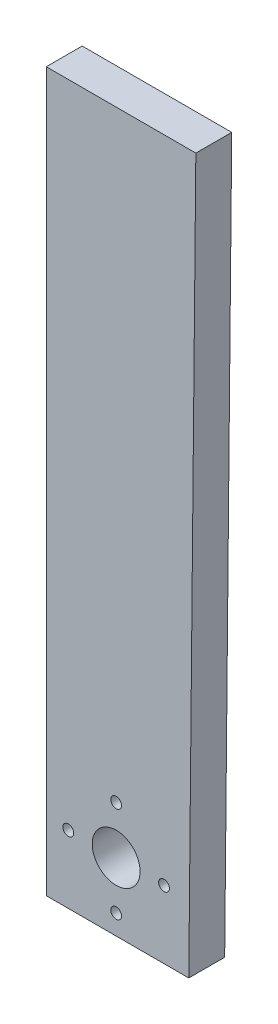
SolidWorks part; units mm, degrees
ref_plane "Plan de face" through (0, 0, 0) normal (0, 0, 1) x (1, 0, 0)
ref_plane "Plan de dessus" through (0, 0, 0) normal (0, 1, 0) x (1, 0, 0)
ref_plane "Plan de droite" through (0, 0, 0) normal (1, 0, 0) x (0, 0, -1)
sketch "Esquisse1" plane through (0, 0, 0) normal (0, 0, 1) x (1, 0, 0)
  line L0 (24.9825, -97.6102) -> (24.9825, 22.3898)
  line L1 (49.9825, 22.3898) -> (24.9825, 22.3898)
  line L2 (49.9825, 22.3898) -> (48.8021, -97.6102)
  line L3 (48.8021, -97.6102) -> (24.9825, -97.6102)
  circle A2 centre (28.664, -86.2754) radius 0.9
  circle A3 centre (36.664, -78.2754) radius 0.9
  circle A4 centre (44.664, -86.2754) radius 0.9
  circle A5 centre (36.664, -94.2754) radius 0.9
  circle A7 centre (36.664, -86.2754) radius 4
  dimension "D3" = 25
  dimension "D6" = 1.8
  dimension "D7" = 1.8
  dimension "D8" = 1.8
  dimension "D9" = 1.8
  dimension "D4" = 8
  dimension "D1" = 120
  dimension "D2" = 120
extrude "Boss.-Extru.1" add sketch "Esquisse1" along normal blind 6
